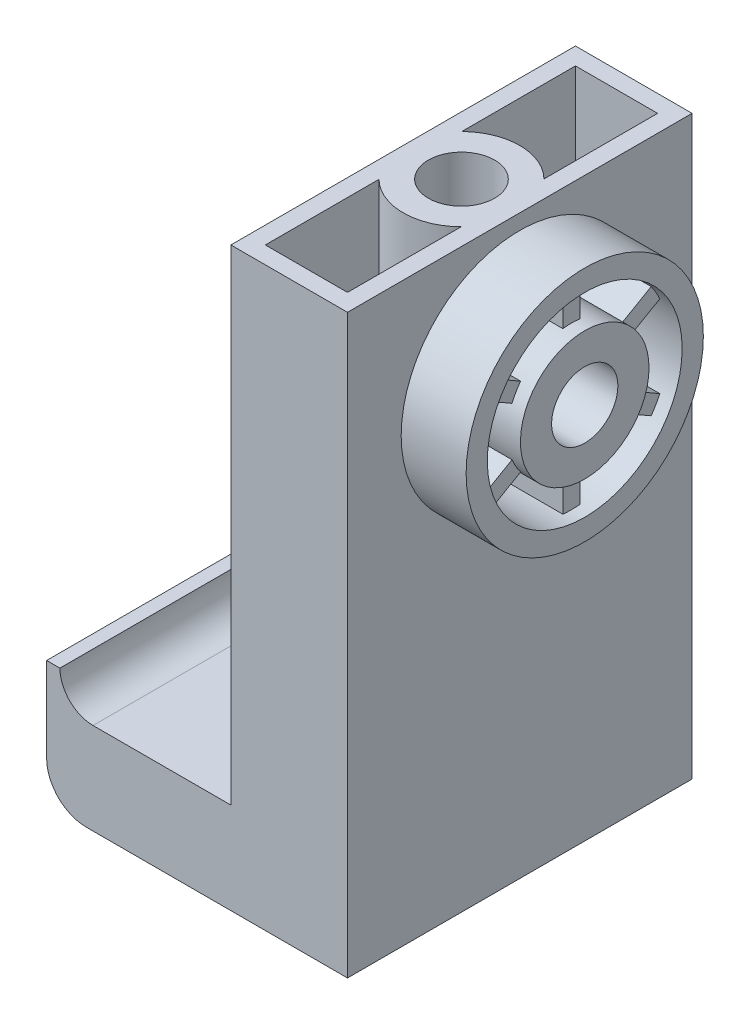
SolidWorks part; units mm, degrees
ref_plane "Front Plane" through (0, 0, 0) normal (0, 0, 1) x (1, 0, 0)
ref_plane "Top Plane" through (0, 0, 0) normal (0, 1, 0) x (1, 0, 0)
ref_plane "Right Plane" through (0, 0, 0) normal (1, 0, 0) x (0, 0, -1)
sketch "Sketch1" plane through (0, 0, 0) normal (0, 0, 1) x (1, 0, 0)
  line L0 (-28.829, 11.938) -> (-27.559, 11.938)
  line L2 (0, 0) -> (0, 55.245)
  line L3 (0, 55.245) -> (-11.176, 55.245)
  line L4 (-11.176, 8.763) -> (-11.176, 55.245)
  line L7 (0, 0) -> (-25.019, 0)
  line L8 (-28.829, 11.938) -> (-28.829, 3.81)
  line L9 (-24.384, 8.763) -> (-11.176, 8.763)
  arc A0 (-27.559, 11.938) -> (-24.384, 8.763) centre (-24.384, 11.938) ccw
  arc A1 (-25.019, 0) -> (-28.829, 3.81) centre (-25.019, 3.81) cw
  point P12 (-28.829, 0)
  dimension "D6" = 1.27
  dimension "D7" = 3.81
  dimension "D1" = 55.245
  dimension "D2" = 28.829
  dimension "D3" = 11.938
  dimension "D4" = 11.176
  dimension "D5" = 8.763
extrude "Boss-Extrude1" add sketch "Sketch1" along normal mid plane 33.02
sketch "Sketch2" plane through (0, 0, 0) normal (1, 0, 0) x (0, 0, -1)
  line L0 (-16.51, 0) -> (16.51, 0) construction
  line L1 (0, 42.418) -> (0, 53.7845) construction
  line L2 (-0.8255, 48.5219) -> (-0.8255, 51.7159)
  line L3 (0.8255, 48.5219) -> (0.8255, 51.7159)
  line L4 (0, 0) -> (0, 42.418) construction
  line L5 (5.6989, 44.7551) -> (8.465, 46.3521)
  line L6 (4.8734, 46.1849) -> (7.6395, 47.7819)
  line L7 (4.8734, 38.6511) -> (7.6395, 37.0541)
  line L8 (5.6989, 40.0809) -> (8.465, 38.4839)
  line L9 (-0.8255, 36.3141) -> (-0.8255, 33.1201)
  line L10 (0.8255, 36.3141) -> (0.8255, 33.1201)
  line L11 (-5.6989, 40.0809) -> (-8.465, 38.4839)
  line L12 (-4.8734, 38.6511) -> (-7.6395, 37.0541)
  line L13 (-4.8734, 46.1849) -> (-7.6395, 47.7819)
  line L14 (-5.6989, 44.7551) -> (-8.465, 46.3521)
  circle A0 centre (0, 42.418) radius 11.3665
  arc A1 (-0.8255, 48.5219) -> (-4.8734, 46.1849) centre (0, 42.418) ccw
  circle A2 centre (0, 42.418) radius 3.175
  arc A3 (-5.6989, 44.7551) -> (-5.6989, 40.0809) centre (0, 42.418) ccw
  arc A4 (-4.8734, 38.6511) -> (-0.8255, 36.3141) centre (0, 42.418) ccw
  arc A5 (0.8255, 36.3141) -> (4.8734, 38.6511) centre (0, 42.418) ccw
  arc A6 (5.6989, 40.0809) -> (5.6989, 44.7551) centre (0, 42.418) ccw
  arc A7 (4.8734, 46.1849) -> (0.8255, 48.5219) centre (0, 42.418) ccw
  arc A8 (-0.8255, 51.7159) -> (-7.6395, 47.7819) centre (0, 42.418) ccw
  arc A9 (-8.465, 46.3521) -> (-8.465, 38.4839) centre (0, 42.418) ccw
  arc A10 (-7.6395, 37.0541) -> (-0.8255, 33.1201) centre (0, 42.418) ccw
  arc A11 (0.8255, 33.1201) -> (7.6395, 37.0541) centre (0, 42.418) ccw
  arc A12 (8.465, 38.4839) -> (8.465, 46.3521) centre (0, 42.418) ccw
  arc A13 (7.6395, 47.7819) -> (0.8255, 51.7159) centre (0, 42.418) ccw
  point P15 (0.8255, 48.5219)
  point P31 (0, 0)
  point P33 (0.8255, 51.7159)
  dimension "D1" = 42.418
  dimension "D2" = 22.733
  dimension "D3" = 12.319
  dimension "D4" = 6.35
  dimension "D7" = 18.669
  dimension "D5" = 0.8255
  dimension "D6" = 6
extrude "Boss-Extrude2" add sketch "Sketch2" along normal blind 6.223
sketch "Sketch3" plane through (0, 0, 0) normal (0, 0, 1) x (1, 0, 0)
  line L0 (6.223, 42.418) -> (-11.176, 42.418) construction
  line L1 (6.223, 31.0515) -> (6.223, 53.7845) construction
  line L2 (-11.176, 55.245) -> (-11.176, 8.763) construction
  line L4 (6.223, 51.7525) -> (4.953, 51.7525)
  line L5 (6.223, 51.7525) -> (6.223, 48.5775)
  line L6 (6.223, 48.5775) -> (4.953, 48.5775)
  line L7 (4.953, 51.7525) -> (4.953, 48.5775)
  dimension "D1" = 1.27
  dimension "D2" = 3.175
  dimension "D3" = 6.1595
revolve "Cut-Revolve1" cut sketch "Sketch3" angle 360 about L0
sketch "Sketch4" plane through (0, 55.245, 0) normal (0, 1, 0) x (1, 0, 0)
  line L4 (-5.588, 16.51) -> (-5.588, -16.51) construction
  line L5 (0, 16.51) -> (-11.176, 16.51) construction
  line L6 (0, -16.51) -> (-11.176, -16.51) construction
  line L8 (-1.651, 14.859) -> (-9.525, 14.859)
  line L9 (-9.525, 14.859) -> (-9.525, -14.859)
  line L10 (-9.525, -14.859) -> (-1.651, -14.859)
  line L11 (-1.651, -14.859) -> (-1.651, 14.859)
  line L12 (-1.651, 14.859) -> (-9.525, 14.859)
  line L13 (-9.525, 14.859) -> (-9.525, -14.859)
  line L14 (-9.525, -14.859) -> (-1.651, -14.859)
  line L15 (-1.651, -14.859) -> (-1.651, 14.859)
  line L16 (0, 0) -> (-11.176, 0) construction
  line L17 (-11.176, -16.51) -> (-11.176, 16.51) construction
  arc A0 (-9.525, -3.9656) -> (-1.651, -3.9656) centre (-5.588, 0) ccw
  circle A1 centre (-5.588, 0) radius 3.175
  arc A2 (-1.651, 3.9656) -> (-9.525, 3.9656) centre (-5.588, 0) ccw
  dimension "D2" = 6.35
  dimension "D1" = 1.651
extrude "Cut-Extrude1" cut sketch "Sketch4" against normal blind 54.61 contours A2 L15 L12 L13 | A0 L13 L14 L15 | A1
